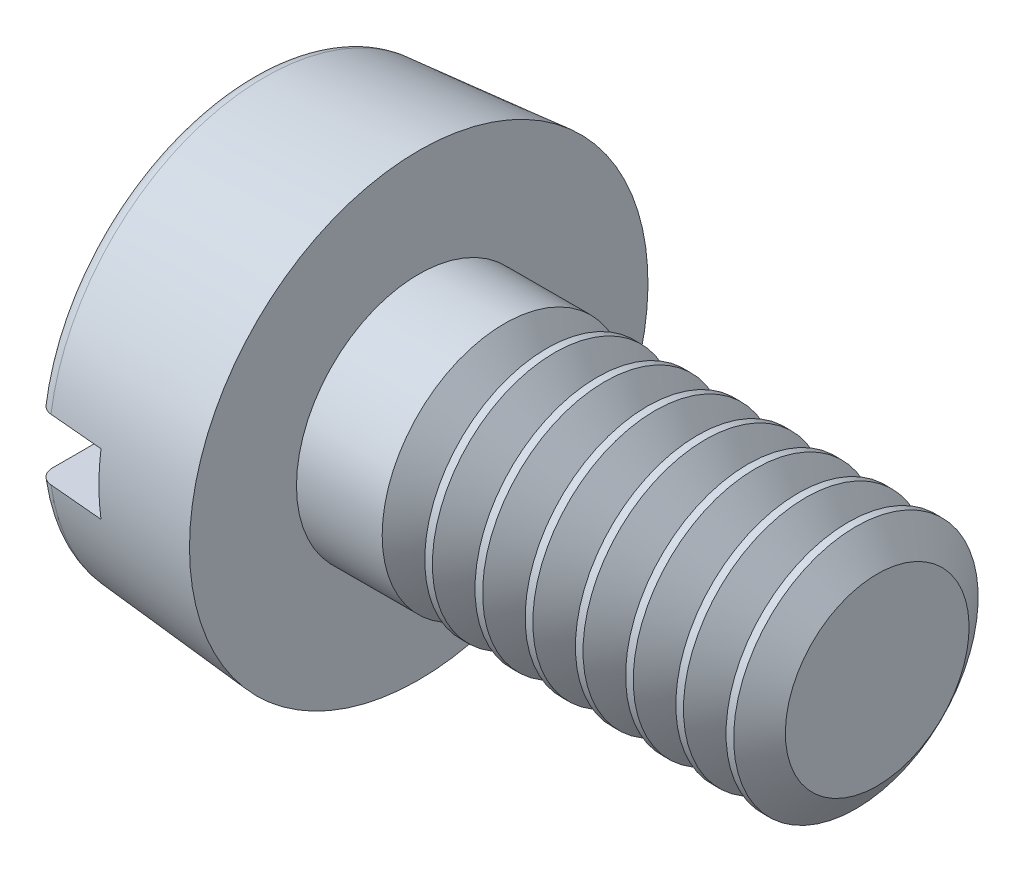
SolidWorks part; units mm, degrees
ref_plane "Plane1" through (0, 0, 0) normal (0, 0, 1) x (1, 0, 0)
ref_plane "Plane2" through (0, 0, 0) normal (0, 1, 0) x (1, 0, 0)
ref_plane "Plane3" through (0, 0, 0) normal (1, 0, 0) x (0, 0, -1)
sketch "BodySke" plane through (0, 0, 0) normal (0, 0, 1) x (1, 0, 0)
  line L0 (1.1, 0.8) -> (1.1, 1.5)
  line L1 (0, 0) -> (0, 1.4038)
  line L2 (-25.4, 0) -> (127, 0) construction
  line L3 (4.1, 0) -> (0, 0)
  line L4 (1.1, 0.8) -> (4.1, 0.8)
  line L5 (4.1, 0.8) -> (4.1, 0)
  line L6 (0, 1.4038) -> (1.1, 1.5)
  line L9 (1.45, 2.3875) -> (1.45, -7.1375) construction
  line L10 (1.1, 6.35) -> (1.1, -3.175) construction
  dimension "Head_ht" = 1.1
  dimension "Diameter" = 1.6
  dimension "Length" = 3
  dimension "Head_dia" = 3
  dimension "Advance" = 0.35
  dimension "Thread_nom" = 3
  dimension "Head_side_angle" = 5
revolve "Base-Revolve" add sketch "BodySke"
cosmetic thread "ThreadCosmetic" [suppressed]
fillet "Fillet1" [suppressed] radius 0.1
fillet "Fillet2" radius 0.1 1 edges at (0, 0, 1.4038)
sketch "Sketch2" plane through (0, 0, 0) normal (1, 0, 0) x (0, 0, -1)
  line L0 (1.5, -0.2) -> (-1.5, -0.2)
  line L1 (1.5, -0.2) -> (1.5, 0.2)
  line L2 (-1.5, 0.2) -> (1.5, 0.2)
  line L3 (-1.5, 0.2) -> (-1.5, -0.2)
  dimension "D1" = 3
  dimension "D2" = 1.5
  dimension "Slot_width" = 0.4
  dimension "D3" = 0.2
extrude "Slot" cut sketch "Sketch2" along normal blind 0.45
sketch "ThdSchSke" plane through (0, 0, 0) normal (0, 0, 1) x (1, 0, 0)
  line L0 (1.8, -0.601) -> (1.6607, -0.8)
  line L1 (1.8, -0.601) -> (1.9393, -0.8)
  line L2 (1.9393, -0.8) -> (1.9393, -1)
  line L3 (-3.175, 0) -> (5.1513, 0) construction
  line L5 (1.9393, -1) -> (1.6607, -1)
  line L6 (1.6607, -1) -> (1.6607, -0.8)
  dimension "Thread_minor" = 1.202
  dimension "Diameter" = 1.6
  dimension "Start" = 1.8
  dimension "SideAngle" = 55
  dimension "VeeAngle" = 70
  dimension "Overcut" = 2
revolve "ThreadSchematic" cut sketch "ThdSchSke" angle 360 about L3
pattern_linear "ThdSchPat" count 8 spacing 0.3286 along (1, 0, 0) of "ThreadSchematic"
equation "\"D1@Sketch2\" = \"Head_dia@BodySke\""
equation "\"D2@Sketch2\" = \"D1@Sketch2\" / 2"
equation "\"D3@Sketch2\" = \"Slot_width@Sketch2\" / 2"
equation "\"Thread_length@ThreadCosmetic\" = ((sgn( (\"Length@BodySke\" - \"Advance@BodySke\" * 2.0 ) - \"Thread_nom@BodySke\" )-1)*( (\"Length@BodySke\" - \"Advance@BodySke\"  * 2.0) - \"Thread_nom@BodySke\" ))/-2+ \"Thread_nom@BodySke\""
equation "\"Thread_minor@ThdSchSke\" = \"Thread_minor@ThreadCosmetic\""
equation "\"Diameter@ThdSchSke\" = \"Diameter@BodySke\""
equation "\"Overcut@ThdSchSke\" = \"Diameter@BodySke\" * 1.25"
equation "\"Start@ThdSchSke\" = \"Head_ht@BodySke\" + \"Length@BodySke\" - \"Thread_length@ThreadCosmetic\"  '---Non-countersunk---"
equation "\"Num_threads@ThdSchPat\" = int( \"Thread_length@ThreadCosmetic\" / \"Advance@BodySke\" + 0.999 )  + 1"
equation "\"Advance@ThdSchPat\" = \"Thread_length@ThreadCosmetic\" /  (\"Num_threads@ThdSchPat\" - 1) 'relax it"
